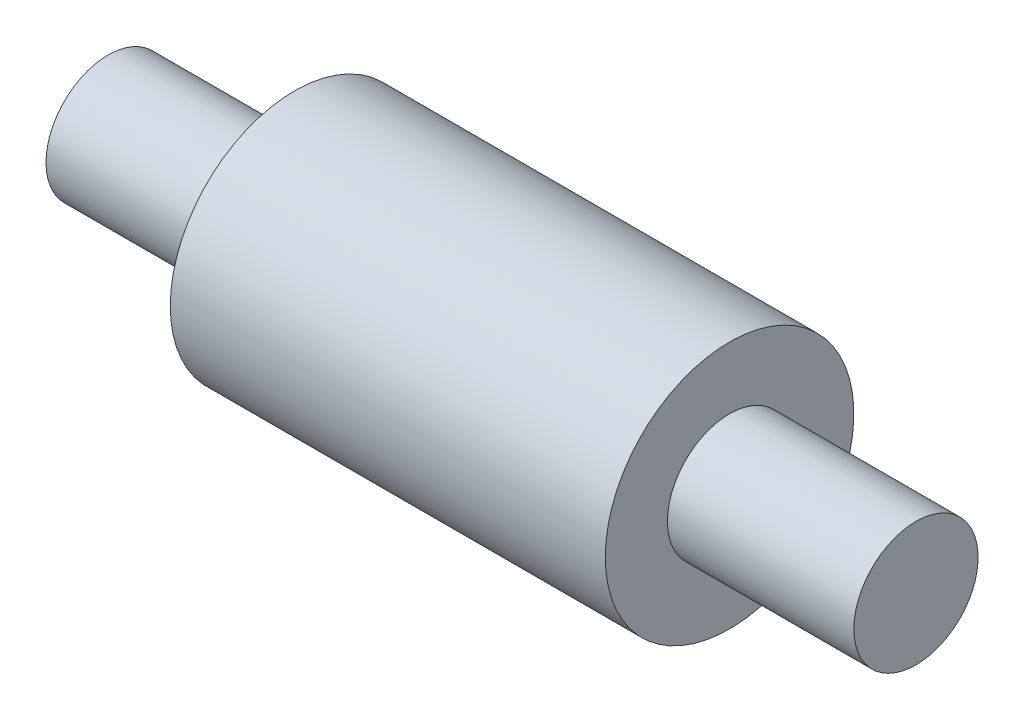
SolidWorks part; units mm, degrees
material "201 Annealed Stainless Steel (SS)"
ref_plane "Front Plane" through (0, 0, 0) normal (0, 0, 1) x (1, 0, 0)
ref_plane "Top Plane" through (0, 0, 0) normal (0, 1, 0) x (1, 0, 0)
ref_plane "Right Plane" through (0, 0, 0) normal (1, 0, 0) x (0, 0, -1)
sketch "Sketch1" plane through (0, 0, 0) normal (0, 0, 1) x (1, 0, 0)
  line L0 (-58.4182, 0) -> (109.1587, 0) construction
  line L1 (0, 0) -> (0, 10)
  line L2 (0, 10) -> (30, 10)
  line L3 (30, 10) -> (30, 20)
  line L4 (30, 20) -> (100, 20)
  line L5 (100, 20) -> (100, 10)
  line L6 (100, 10) -> (130, 10)
  line L7 (130, 10) -> (130, 0)
  line L8 (130, 0) -> (0, 0)
  dimension "D1" = 30
  dimension "D2" = 100
revolve "Revolve2" add sketch "Sketch1" angle 360 about L0
